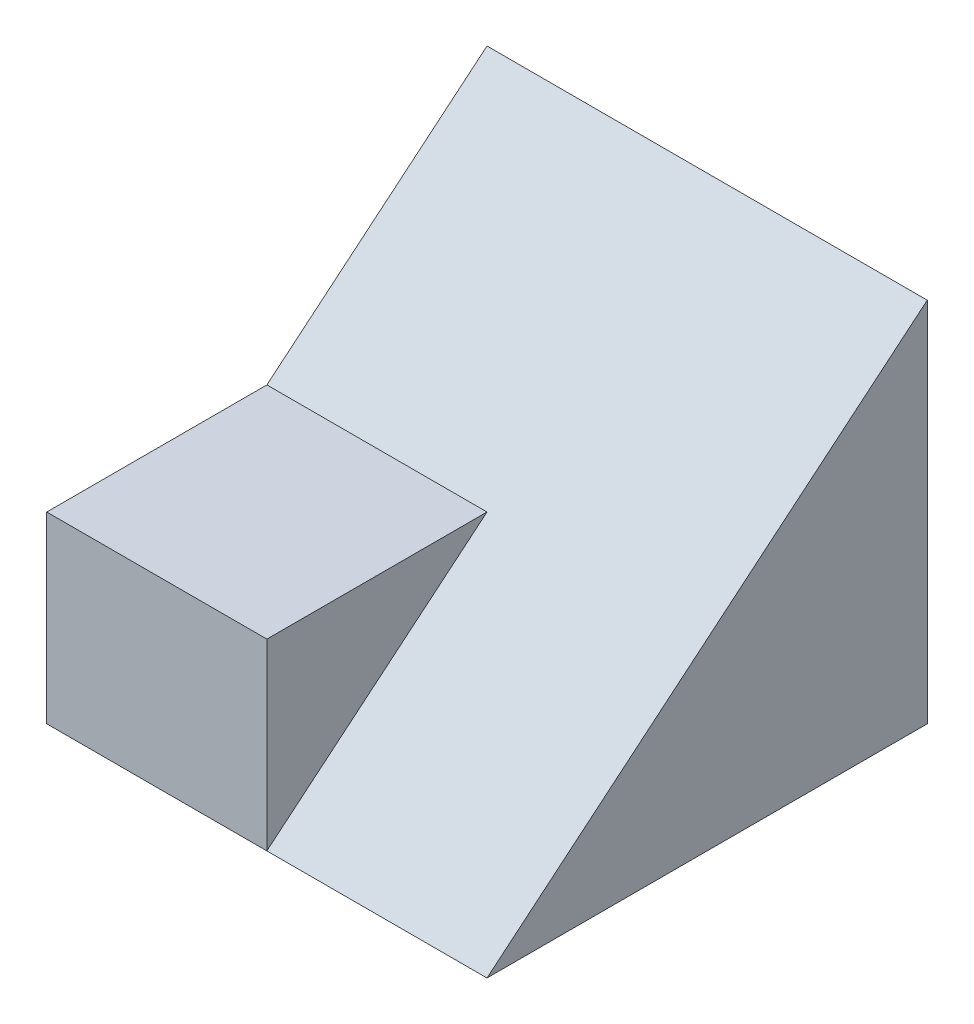
SolidWorks part; units mm, degrees
ref_plane "Front" through (0, 0, 0) normal (0, 0, 1) x (1, 0, 0)
ref_plane "Top" through (0, 0, 0) normal (0, 1, 0) x (1, 0, 0)
ref_plane "Right" through (0, 0, 0) normal (1, 0, 0) x (0, 0, -1)
sketch "Sketch1" plane through (0, 0, 0) normal (0, 1, 0) x (1, 0, 0)
  line L1 (-3, -3) -> (3, -3)
  line L2 (-3, -3) -> (-3, 3)
  line L3 (-3, 3) -> (3, 3)
  line L4 (3, -3) -> (3, 3)
  line L5 (-3, -3) -> (3, 3) construction
  line L6 (-3, 3) -> (3, -3) construction
  point P0 (0, 0)
  dimension "D1" = 6
  dimension "D2" = 6
extrude "Boss-Extrude1" add sketch "Sketch1" along normal blind 5
sketch "Sketch2" plane through (-3, 0, 0) normal (-1, 0, 0) x (0, 0, 1)
  line L0 (-3, 5) -> (0, 2.5)
  line L1 (0, 2.5) -> (3, 2.5)
  line L4 (-3, 0) -> (3, 0)
  line L5 (3, 0) -> (3, 5)
  line L6 (3, 5) -> (-3, 5)
  line L7 (-3, 5) -> (-3, 0)
  line L8 (-3, 0) -> (3, 0)
  line L9 (3, 0) -> (3, 5)
  line L10 (3, 5) -> (-3, 5)
  line L11 (-3, 5) -> (-3, 0)
  dimension "D2" = 3
  dimension "D1" = 0
extrude "Cut-Extrude1" cut sketch "Sketch2" against normal blind 10
sketch "Sketch3" plane through (3, 0, 0) normal (1, 0, 0) x (0, 0, -1)
  line L0 (3, 5) -> (-3, 0)
  line L6 (3, 5) -> (0, 2.5)
  line L7 (3, 5) -> (0, 2.5)
  line L8 (-3, 2.5) -> (-3, 0)
  line L9 (-3, 0) -> (3, 0)
  line L10 (3, 0) -> (3, 5)
  line L11 (0, 2.5) -> (-3, 2.5)
  line L12 (0, 2.5) -> (-3, 2.5)
  line L13 (-3, 2.5) -> (-3, 0)
  line L14 (-3, 0) -> (3, 0)
  line L15 (3, 0) -> (3, 5)
  dimension "D1" = 0
extrude "Cut-Extrude2" cut sketch "Sketch3" against normal blind 3
